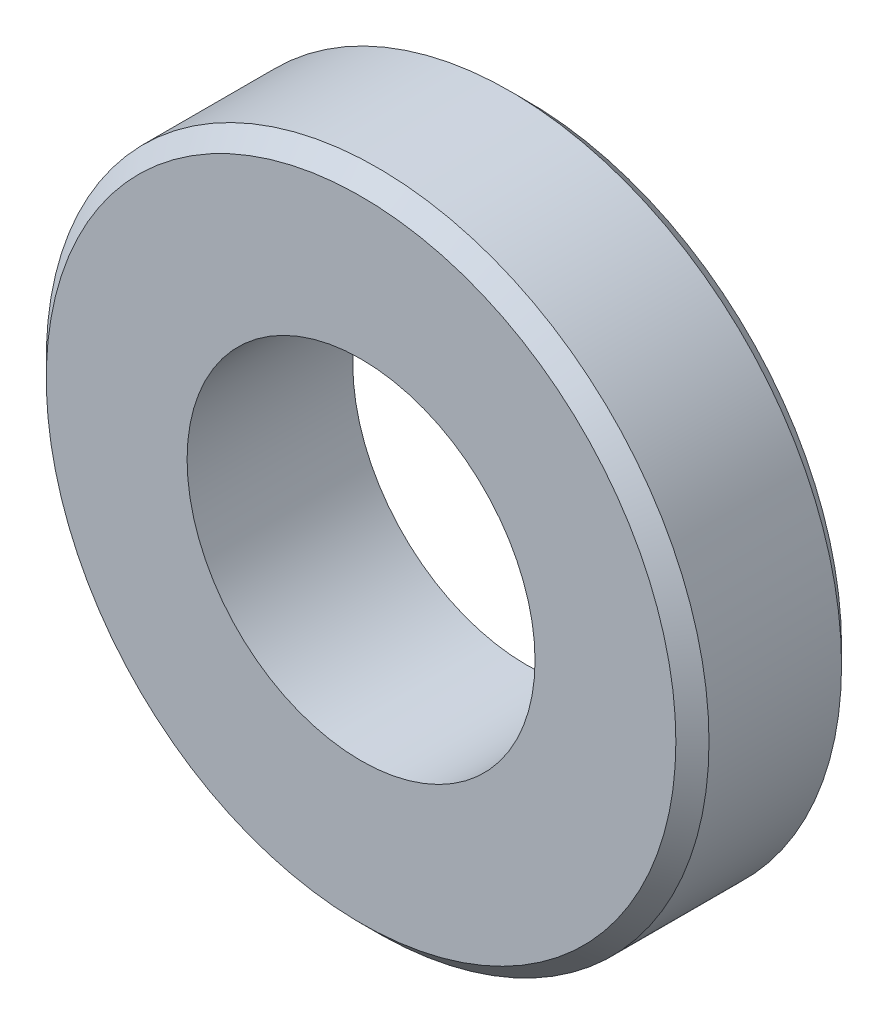
SolidWorks part; units mm, degrees
material "POM Acetal Coopolymer聚甲醛树脂"
ref_plane "前视基准面" through (0, 0, 0) normal (0, 0, 1) x (1, 0, 0)
ref_plane "上视基准面" through (0, 0, 0) normal (0, 1, 0) x (1, 0, 0)
ref_plane "右视基准面" through (0, 0, 0) normal (1, 0, 0) x (0, 0, -1)
sketch "草图1" plane through (0, 0, 0) normal (0, 0, 1) x (1, 0, 0)
  circle A0 centre (0, 0) radius 2.1
  circle A1 centre (0, 0) radius 4
  dimension "D1" = 4.2
  dimension "D2" = 8
extrude "凸台-拉伸1" add sketch "草图1" along normal mid plane 2
chamfer "倒角1" distance 0.2 angle 45 2 edges at (4, 0, -1) (4, 0, 1)
